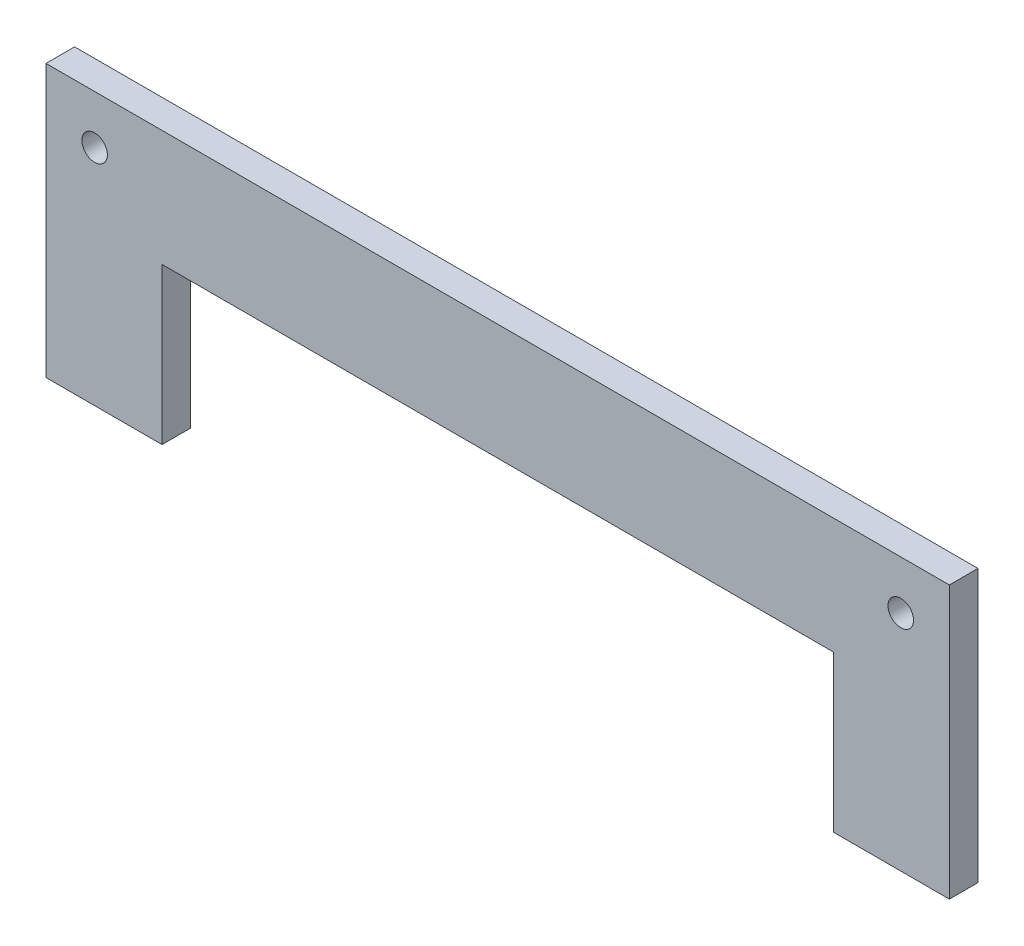
SolidWorks part; units mm, degrees
material "Maple"
ref_plane "Front Plane" through (0, 0, 0) normal (0, 0, 1) x (1, 0, 0)
ref_plane "Top Plane" through (0, 0, 0) normal (0, 1, 0) x (1, 0, 0)
ref_plane "Right Plane" through (0, 0, 0) normal (1, 0, 0) x (0, 0, -1)
sketch "Sketch1" plane through (0, 0, 0) normal (0, 0, 1) x (1, 0, 0)
  line L0 (-50, 0) -> (50, 0) construction
  line L1 (-50, 0) -> (-50, -30) construction
  line L2 (-50, -30) -> (-37.3, -30) construction
  line L3 (-37.3, -30) -> (-37.3, -12.7) construction
  line L4 (-37.3, -12.7) -> (37.3, -12.7) construction
  line L5 (37.3, -12.7) -> (37.3, -30) construction
  line L6 (37.3, -30) -> (50, -30) construction
  line L7 (50, -30) -> (50, 0) construction
  line L8 (-50, 0) -> (-44.6967, -5.3033) construction
  line L9 (0, 0) -> (0, -7.781) construction
  line L10 (50.085, -30.085) -> (50.085, 0.085)
  line L11 (-50.085, 0.085) -> (50.085, 0.085)
  line L12 (-50.085, 0.085) -> (-50.085, -30.085)
  line L13 (-50.085, -30.085) -> (-37.215, -30.085)
  line L14 (-37.215, -30.085) -> (-37.215, -12.785)
  line L15 (-37.215, -12.785) -> (37.215, -12.785)
  line L16 (37.215, -12.785) -> (37.215, -30.085)
  line L17 (37.215, -30.085) -> (50.085, -30.085)
  circle A0 centre (-44.6967, -5.3033) radius 1.415
  circle A1 centre (44.6967, -5.3033) radius 1.415
  point P4 (0, 0)
  dimension "D7" = 2.83
  dimension "D1" = 100
  dimension "D2" = 30
  dimension "D3" = 12.7
  dimension "D4" = 12.7
  dimension "D5" = 45
  dimension "D6" = 7.5
  dimension "D8" = 0.085
extrude "Boss-Extrude1" add sketch "Sketch1" along normal blind 3.175
equation "\"kerf\"= 0.17 / 2"
equation "\"D8@Sketch1\"=\"kerf\""
equation "\"D7@Sketch1\"=3 - 2*(\"kerf\")"
